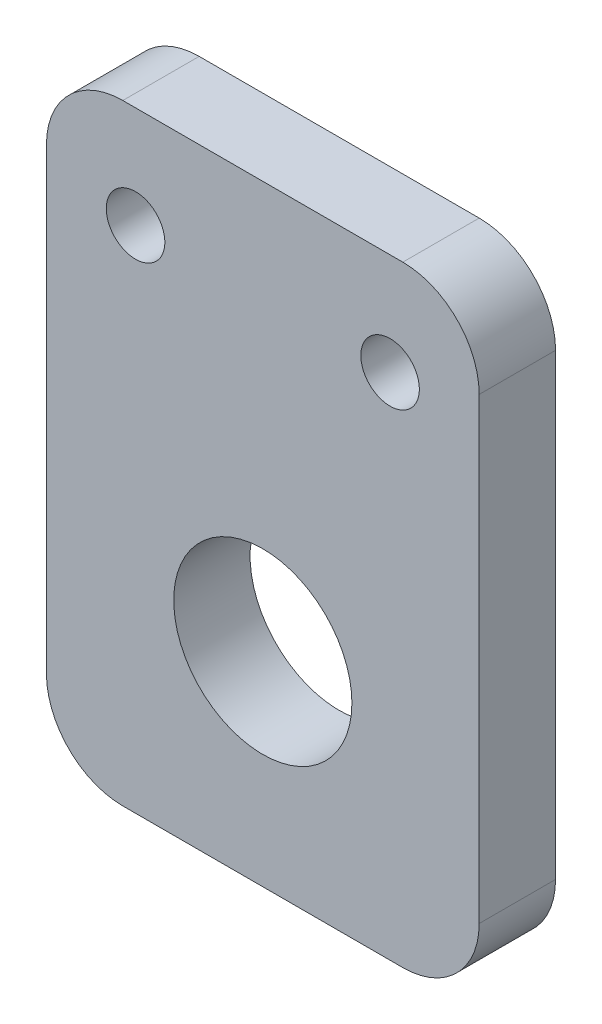
SolidWorks part; units mm, degrees
material "A-玻璃纤维"
ref_plane "前视基准面" through (0, 0, 0) normal (0, 0, 1) x (1, 0, 0)
ref_plane "上视基准面" through (0, 0, 0) normal (0, 1, 0) x (1, 0, 0)
ref_plane "右视基准面" through (0, 0, 0) normal (1, 0, 0) x (0, 0, -1)
sketch "草图1" plane through (0, 0, 0) normal (0, 0, 1) x (1, 0, 0)
  line L0 (0, 37.1943) -> (0, -40.6732) construction
  line L1 (64.5655, 0) -> (-67.8399, 0) construction
  line L3 (-8.5, 0) -> (8.5, 0)
  line L4 (-8.5, 0) -> (-8.5, 24)
  line L5 (-8.5, 24) -> (8.5, 24)
  line L6 (8.5, 0) -> (8.5, 24)
  circle A0 centre (0, 8) radius 3.5
  circle A2 centre (5, 20) radius 1.15
  circle A3 centre (-5, 20) radius 1.15
  dimension "D1" = 7
  dimension "D2" = 2.3
  dimension "D3" = 10
  dimension "D4" = 4
  dimension "D5" = 8
  dimension "D6" = 12
  dimension "D7" = 17
extrude "凸台-拉伸1" add sketch "草图1" along normal blind 3
fillet "圆角1" radius 3 4 edges at (-8.5, 0, 1.5) (8.5, 0, 1.5) (8.5, 24, 1.5) (-8.5, 24, 1.5)
